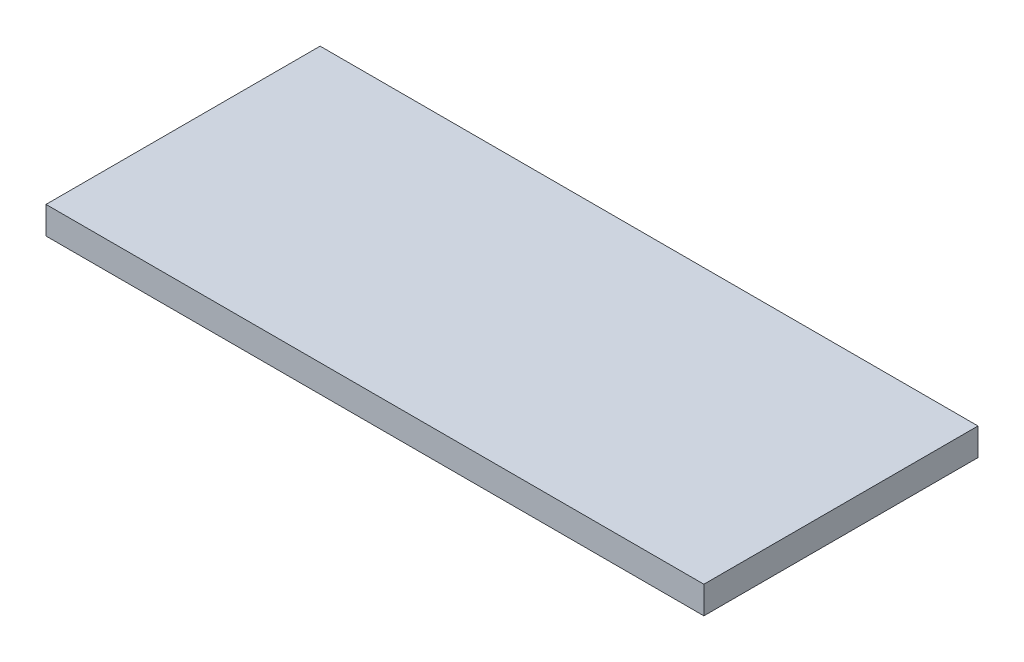
SolidWorks part; units mm, degrees
ref_plane "Alzado" through (0, 0, 0) normal (0, 0, 1) x (1, 0, 0)
ref_plane "Planta" through (0, 0, 0) normal (0, 1, 0) x (1, 0, 0)
ref_plane "Vista lateral" through (0, 0, 0) normal (1, 0, 0) x (0, 0, -1)
sketch "Croquis1" plane through (0, 0, 0) normal (0, 1, 0) x (1, 0, 0)
  line L1 (-76.2, 31.75) -> (76.2, 31.75)
  line L2 (-76.2, 31.75) -> (-76.2, -31.75)
  line L3 (-76.2, -31.75) -> (76.2, -31.75)
  line L4 (76.2, 31.75) -> (76.2, -31.75)
  line L5 (-76.2, 31.75) -> (76.2, -31.75) construction
  line L6 (-76.2, -31.75) -> (76.2, 31.75) construction
  point P0 (0, 0)
  dimension "D1" = 152.4
  dimension "D2" = 63.5
extrude "Saliente-Extruir1" add sketch "Croquis1" along normal blind 6.35
